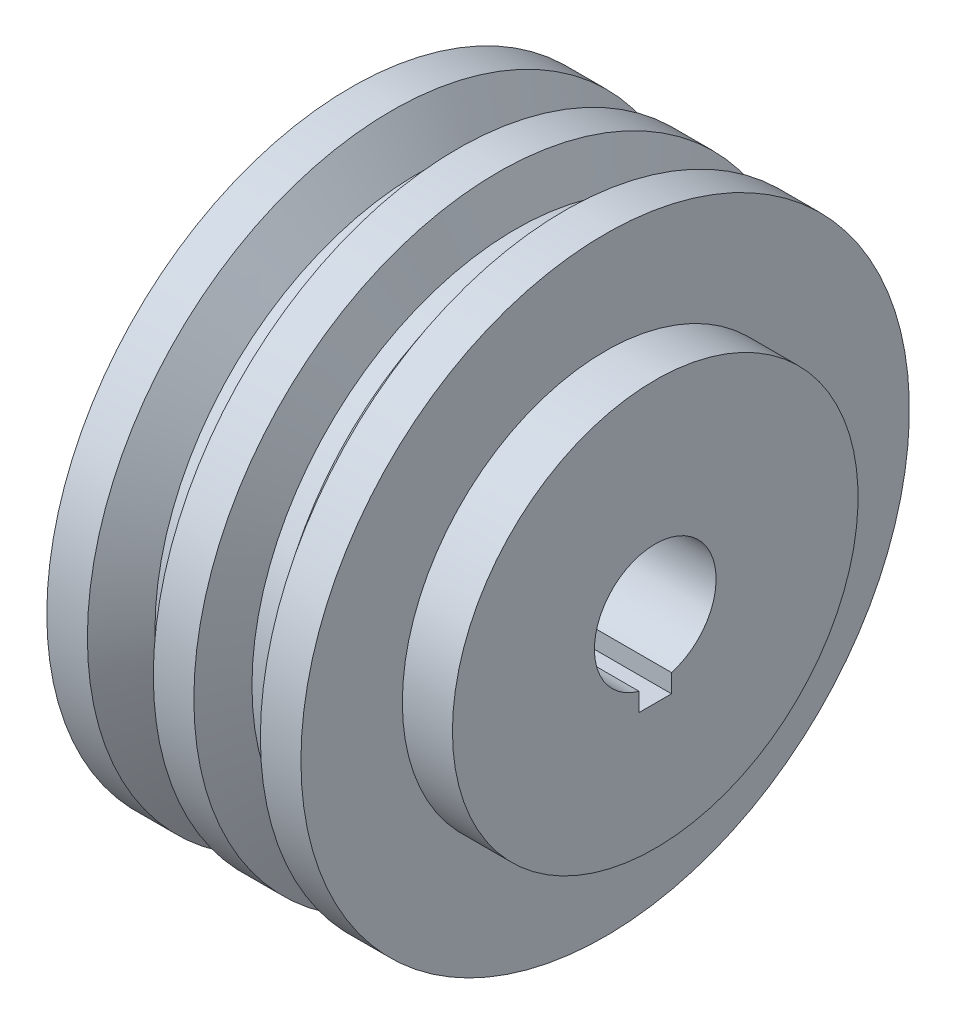
SolidWorks part; units mm, degrees
ref_plane "Front Plane" through (0, 0, 0) normal (0, 0, 1) x (1, 0, 0)
ref_plane "Top Plane" through (0, 0, 0) normal (0, 1, 0) x (1, 0, 0)
ref_plane "Right Plane" through (0, 0, 0) normal (1, 0, 0) x (0, 0, -1)
sketch "Sketch1" plane through (0, 0, 0) normal (0, 0, 1) x (1, 0, 0)
  line L0 (0, 0) -> (75, 0) construction
  line L1 (75, -15) -> (10, -15)
  line L2 (62.6462, -75) -> (62.6462, -50)
  line L3 (52.6462, -75) -> (62.6462, -75)
  line L4 (52.6462, -75) -> (45.2113, -65)
  line L5 (45.2113, -65) -> (40.5713, -65)
  line L6 (40.5713, -65) -> (36.2502, -75)
  line L7 (36.2502, -75) -> (26.2502, -75)
  line L8 (26.2502, -75) -> (21.3, -65)
  line L9 (21.3, -65) -> (16.66, -65)
  line L10 (16.66, -65) -> (10, -75)
  line L11 (10, -75) -> (0, -75)
  line L12 (0, -75) -> (0, -70)
  line L13 (0, -70) -> (10, -15)
  line L14 (62.6462, -50) -> (75, -50)
  line L15 (75, -15) -> (75, -50)
  dimension "D1" = 30
  dimension "D2" = 10
  dimension "D3" = 150
  dimension "D4" = 55
  dimension "D5" = 10
  dimension "D6" = 10
  dimension "D7" = 10
  dimension "D8" = 60
  dimension "D9" = 4.64
  dimension "D10" = 10
  dimension "D11" = 10
  dimension "D12" = 10
  dimension "D13" = 4.64
  dimension "D14" = 10
  dimension "D15" = 60
  dimension "D16" = 100
  dimension "D17" = 65
  dimension "D18" = 12.3538
  dimension "D19" = 36.63
revolve "Revolve1" add sketch "Sketch1" angle 360 about L0
sketch "Sketch2" plane through (75, 0, 0) normal (1, 0, 0) x (0, 0, -1)
  line L0 (0, 0) -> (0, -15) construction
  line L1 (4, -19) -> (-4, -19)
  line L2 (4, -19) -> (4, -11)
  line L3 (4, -11) -> (-4, -11)
  line L4 (-4, -19) -> (-4, -11)
  line L5 (4, -19) -> (-4, -11) construction
  line L6 (4, -11) -> (-4, -19) construction
  circle A0 centre (0, 0) radius 15 construction
  point P0 (0, -15)
  dimension "D1" = 8
  dimension "D2" = 8
extrude "Cut-Extrude1" cut sketch "Sketch2" against normal through all
